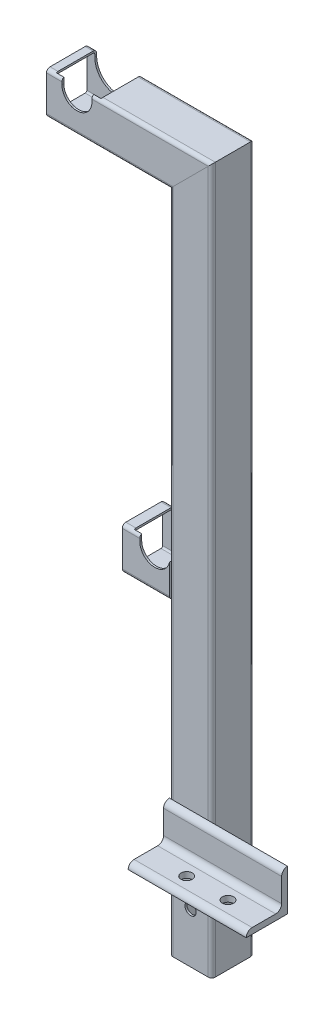
SolidWorks part; units mm, degrees
ref_plane "Front Plane" through (0, 0, 0) normal (0, 0, 1) x (1, 0, 0)
ref_plane "Top Plane" through (0, 0, 0) normal (0, 1, 0) x (1, 0, 0)
ref_plane "Right Plane" through (0, 0, 0) normal (1, 0, 0) x (0, 0, -1)
sketch "Sketch1" plane through (0, 0, 0) normal (0, 0, 1) x (1, 0, 0)
  line L0 (348.3375, 0) -> (348.3375, 500)
  line L1 (348.3375, 500) -> (226.2375, 500)
  line L2 (348.3375, 0) -> (348.3375, -80)
  line L3 (330.4375, 157.0549) -> (330.4375, -80) construction
  line L4 (335.2, 157.0549) -> (335.2, -80) construction
  line L5 (348.3375, 157.0549) -> (348.3375, -80) construction
  line L6 (348.3375, 198) -> (290.4375, 198)
  dimension "D1" = 500
  dimension "D2" = 80
  dimension "D3" = 122.1
  dimension "D4" = 4.7625
  dimension "D5" = 17.9
  dimension "D6" = 335.2
  dimension "D7" = 198
  dimension "D8" = 57.9
other "Structural MemberMain"
ref_plane "Plane1" through (348.3375, 0, 0) normal (0, 1, 0) x (-1, 0, 0)
sketch "Sketch11" plane through (348.3375, 0, 0) normal (0, 1, 0) x (-1, 0, 0)
  line L0 (-14.9, 16.3) -> (14.9, 16.3)
  line L1 (-14.9, 17.9) -> (14.9, 17.9)
  line L2 (-17.9, 14.9) -> (-17.9, -14.9)
  line L3 (-14.9, -17.9) -> (14.9, -17.9)
  line L4 (17.9, 14.9) -> (17.9, -14.9)
  line L5 (-17.9, 17.9) -> (17.9, -17.9) construction
  line L6 (-17.9, -17.9) -> (17.9, 17.9) construction
  line L7 (16.3, 14.9) -> (16.3, -14.9)
  line L8 (-14.9, -16.3) -> (14.9, -16.3)
  line L9 (-16.3, 14.9) -> (-16.3, -14.9)
  arc A0 (-17.9, -14.9) -> (-14.9, -17.9) centre (-14.9, -14.9) ccw
  arc A1 (14.9, -17.9) -> (17.9, -14.9) centre (14.9, -14.9) ccw
  arc A2 (17.9, 14.9) -> (14.9, 17.9) centre (14.9, 14.9) ccw
  arc A3 (-14.9, 17.9) -> (-17.9, 14.9) centre (-14.9, 14.9) ccw
  arc A4 (16.3, 14.9) -> (14.9, 16.3) centre (14.9, 14.9) ccw
  arc A5 (14.9, -16.3) -> (16.3, -14.9) centre (14.9, -14.9) ccw
  arc A6 (-16.3, -14.9) -> (-14.9, -16.3) centre (-14.9, -14.9) ccw
  arc A7 (-14.9, 16.3) -> (-16.3, 14.9) centre (-14.9, 14.9) ccw
  point P0 (0, 0)
  point P30 (0, 0)
  dimension "D3" = 3
  dimension "D1" = 35.8
  dimension "D2" = 35.8
  dimension "D4" = 1.6
sketch "Sketch12" plane through (0, 0, 0) normal (0, 0, 1) x (1, 0, 0)
  line L1 (252, 512.7) -> (252, 523.1) construction
  line L2 (239.3, 512.7) -> (239.3, 523.1)
  line L3 (264.7, 512.7) -> (264.7, 523.1)
  line L4 (348.3375, 500) -> (226.2375, 500) construction
  line L5 (226.2375, 517.9) -> (366.2375, 517.9) construction
  arc A0 (239.3, 512.7) -> (264.7, 512.7) centre (252, 512.7) ccw
  arc A1 (264.7, 523.1) -> (239.3, 523.1) centre (252, 523.1) ccw
  point P2 (252, 517.9)
  dimension "D1" = 25.4
  dimension "D2" = 252
extrude "Cut-ExtrudeTopRailGuide" cut sketch "Sketch12" against normal through all and the other way through all
sketch "Sketch13" plane through (0, 0, 0) normal (0, 1, 0) x (1, 0, 0)
  line L0 (330.4375, -17.9) -> (430.4375, -17.9)
  line L1 (264.7, -17.9) -> (363.2375, -17.9) construction
  line L2 (330.4375, -14.9) -> (330.4375, 14.9) construction
  point P4 (380.4375, -17.9)
  dimension "D1" = 100
other "Structural MemberAngle"
ref_plane "Plane2" through (330.4375, 0, 17.9) normal (1, 0, 0) x (0, 1, 0)
sketch "Sketch14" plane through (330.4375, 0, 17.9) normal (1, 0, 0) x (0, 1, 0)
  line L0 (0, 0) -> (0, 35)
  line L1 (0, 17.5) -> (5, 17.5) construction
  line L2 (5, 30) -> (5, 10)
  line L3 (10, 5) -> (30, 5)
  line L4 (17.5, 5) -> (17.5, 0) construction
  line L5 (35, 0) -> (0, 0)
  arc A0 (35, 0) -> (30, 5) centre (30, 0) ccw
  arc A1 (0, 35) -> (5, 30) centre (0, 30) cw
  arc A2 (10, 5) -> (5, 10) centre (10, 10) cw
  point P10 (17.5, 0)
  point P14 (0, 17.5)
  point P15 (5, 17.5)
  point P16 (17.5, 5)
  point P17 (5, 35)
  point P18 (35, 5)
  point P21 (0, 0)
  dimension "D2" = 5
  dimension "D3" = 35
  dimension "Radius_1" = 5
  dimension "D1" = 5
sketch "Sketch15" plane through (0, 0, 0) normal (0, 1, 0) x (1, 0, 0)
  line L0 (380.4375, -17.9) -> (380.4375, -52.9) construction
  line L1 (430.4375, -52.9) -> (330.4375, -52.9) construction
  line L2 (-65.8005, -37.9) -> (826.6755, -37.9) construction
  line L3 (330.4375, -17.9) -> (430.4375, -17.9) construction
  line L4 (0, 28.933) -> (0, -28.933) construction
  circle A0 centre (299.4, -37.9) radius 4.7625 construction
  circle A1 centre (335.2, -37.9) radius 5.0441 construction
  circle A2 centre (365, -37.9) radius 4.7625
  circle A3 centre (400, -37.9) radius 4.7625
  point P7 (380.4375, -37.9)
  point P16 (0, 0)
  dimension "D2" = 9.525
  dimension "D1" = 20
  dimension "D3" = 335.2
  dimension "D4" = 35.8
  dimension "D5" = 35
  dimension "D6" = 400
extrude "Cut-ExtrudeMountingHoles" cut sketch "Sketch15" along normal through all
sketch "Sketch16" plane through (0, 0, 0) normal (0, 0, 1) x (1, 0, 0)
  line L4 (271.05, 512.7) -> (271.05, 523.1)
  line L5 (232.95, 523.1) -> (232.95, 512.7)
  line L6 (271.05, 512.7) -> (271.05, 523.1)
  line L7 (232.95, 523.1) -> (232.95, 512.7)
  arc A4 (232.95, 512.7) -> (271.05, 512.7) centre (252, 512.7) ccw
  arc A5 (271.05, 523.1) -> (232.95, 523.1) centre (252, 523.1) ccw
  arc A6 (232.95, 512.7) -> (271.05, 512.7) centre (252, 512.7) ccw
  arc A7 (271.05, 523.1) -> (232.95, 523.1) centre (252, 523.1) ccw
  dimension "D1" = 6.35
extrude "Cut-ExtrudeEnlargeRailGuide" cut sketch "Sketch16" against normal through all and the other way up to surface other way up to face at (269.6437, 505.3125, 16.3)
sketch "Sketch18" plane through (0, 0, 17.9) normal (0, 0, 1) x (1, 0, 0)
  line L0 (318, 210.7) -> (318, 221.1) construction
  line L1 (305.3, 210.7) -> (305.3, 221.1)
  line L2 (330.7, 210.7) -> (330.7, 221.1)
  line L3 (290.4375, 215.9) -> (330.4375, 215.9) construction
  line L5 (348.3375, 198) -> (290.4375, 198) construction
  arc A0 (305.3, 210.7) -> (330.7, 210.7) centre (318, 210.7) ccw
  arc A1 (330.7, 221.1) -> (305.3, 221.1) centre (318, 221.1) ccw
  point P2 (318, 215.9)
  dimension "D1" = 25.4
  dimension "D2" = 12.7
  dimension "D3" = 318
extrude "Cut-Extrude2" cut sketch "Sketch18" against normal through all
sketch "Sketch19" plane through (0, 0, 17.9) normal (0, 0, 1) x (1, 0, 0)
  line L0 (348.3375, 0) -> (348.3375, -80) construction
  line L1 (330.4375, 0) -> (430.4375, 0) construction
  line L2 (366.2375, 0) -> (366.2375, -80) construction
  circle A0 centre (348.3375, -37.5) radius 4.7625
  dimension "D1" = 9.525
  dimension "D3" = 17.9
  dimension "D2" = 37.5
extrude "Cut-Extrude3" cut sketch "Sketch19" against normal through all
sketch "Sketch20" plane through (0, 0, -17.9) normal (0, 0, -1) x (-1, 0, 0)
  line L4 (-337.05, 221.1) -> (-337.05, 210.7)
  line L5 (-298.95, 210.7) -> (-298.95, 221.1)
  line L6 (-337.05, 221.1) -> (-337.05, 210.7)
  line L7 (-298.95, 210.7) -> (-298.95, 221.1)
  arc A4 (-337.05, 210.7) -> (-298.95, 210.7) centre (-318, 210.7) ccw
  arc A5 (-298.95, 221.1) -> (-337.05, 221.1) centre (-318, 221.1) ccw
  arc A6 (-337.05, 210.7) -> (-298.95, 210.7) centre (-318, 210.7) ccw
  arc A7 (-298.95, 221.1) -> (-337.05, 221.1) centre (-318, 221.1) ccw
  dimension "D1" = 6.35
extrude "Cut-Extrude4" cut sketch "Sketch20" against normal up to surface (34.2 mm away)
